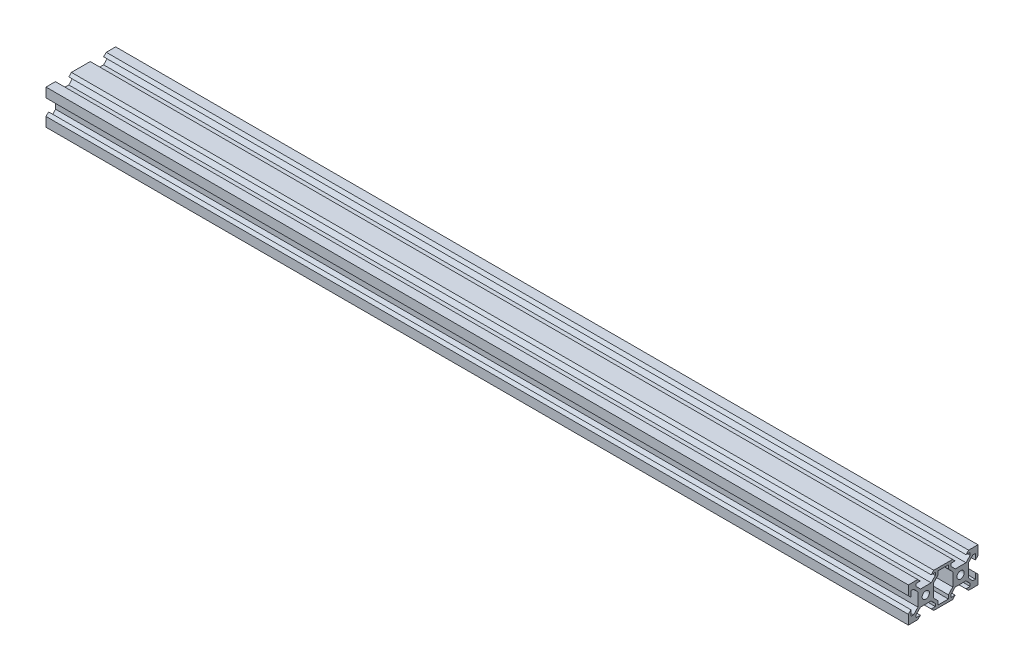
SolidWorks part; units mm, degrees
material "6061-T6 (SS)"
ref_plane "Front Plane" through (0, 0, 0) normal (0, 0, 1) x (1, 0, 0)
ref_plane "Top Plane" through (0, 0, 0) normal (0, 1, 0) x (1, 0, 0)
ref_plane "Right Plane" through (0, 0, 0) normal (1, 0, 0) x (0, 0, -1)
sketch "Sketch1" plane through (0, 0, 0) normal (1, 0, 0) x (0, 0, -1)
  line L136 (-20, -10) -> (-20, -4.6)
  line L147 (-20, -10) -> (20, -10) construction
  line L149 (-20, -10) -> (-20, 10) construction
  line L155 (-20, 10) -> (20, 10) construction
  line L156 (20, -10) -> (20, 10) construction
  line L162 (-20, -10) -> (20, 10) construction
  line L163 (-20, 10) -> (20, -10) construction
  line L177 (-20, -4.6) -> (-18.5, -3.1)
  line L180 (-14.5, -3.7924) -> (-14.5, 3.7924)
  line L181 (0, 0) -> (-20, 0) construction
  line L182 (0, 0) -> (0, -10) construction
  line L184 (-20, -10) -> (-14.6, -10)
  line L185 (-14.6, -10) -> (-13.1, -8.5)
  line L186 (-13.1, -8.5) -> (-15.5, -8.5)
  line L187 (-15.5, -8.5) -> (-15.5, -7)
  line L188 (-15.5, -7) -> (-13.1, -4.5)
  line L189 (-13.1, -4.5) -> (-6.9, -4.5)
  line L190 (-6.9, -4.5) -> (-4.5, -7)
  line L191 (-4.5, -7) -> (-4.5, -8.5)
  line L192 (-4.5, -8.5) -> (-6.9, -8.5)
  line L193 (-6.9, -8.5) -> (-5.4, -10)
  line L194 (-5.4, -10) -> (5.4, -10)
  line L195 (-3, -8.5) -> (-3, -6.3965)
  line L196 (-3, -8.5) -> (3, -8.5)
  line L197 (0, -8.5) -> (0, -10)
  line L201 (-14.5, 0) -> (-12.1, 0) construction
  line L203 (-7.9, 0) -> (-5.5, 0) construction
  line L204 (-5.5, 3.7924) -> (-5.5, -3.7924)
  line L205 (-5.5, -3.7924) -> (-3, -6.3965)
  line L206 (-13.1, -4.5) -> (-13.1, -8.5) construction
  line L207 (-13.1, -8.5) -> (-6.9, -8.5) construction
  line L208 (-6.9, -4.5) -> (-6.9, -8.5) construction
  line L209 (-18.5, -3.1) -> (-18.5, -6.3965)
  line L210 (-18.5, -6.3965) -> (-17, -6.3965)
  line L211 (-15.5, -7) -> (-4.5, -7) construction
  line L212 (-17, -6.3965) -> (-14.5, -3.7924)
  line L213 (-13.1, -4.5) -> (-6.9, -4.5) construction
  line L214 (-10, -4.5) -> (-10, 0) construction
  line L215 (-18.5, -6.3965) -> (-20, -6.3965) construction
  line L216 (-15.5, -8.5) -> (-15.5, -10) construction
  line L217 (-4.5, -8.5) -> (-4.5, -10) construction
  line L218 (-17, -6.3965) -> (-3, -6.3965) construction
  line L219 (-18.5, -3.1) -> (-20, -3.1) construction
  line L220 (-18.5, 6.3965) -> (-17, 6.3965)
  line L221 (-18.5, 3.1) -> (-18.5, 6.3965)
  line L222 (-20, 4.6) -> (-18.5, 3.1)
  line L223 (-20, 10) -> (-20, 4.6)
  line L224 (-20, 10) -> (-14.6, 10)
  line L225 (-14.6, 10) -> (-13.1, 8.5)
  line L226 (-13.1, 8.5) -> (-15.5, 8.5)
  line L227 (-15.5, 8.5) -> (-15.5, 7)
  line L228 (-15.5, 7) -> (-13.1, 4.5)
  line L229 (-13.1, 4.5) -> (-6.9, 4.5)
  line L230 (-6.9, 4.5) -> (-4.5, 7)
  line L231 (-4.5, 7) -> (-4.5, 8.5)
  line L232 (-4.5, 8.5) -> (-6.9, 8.5)
  line L233 (-6.9, 8.5) -> (-5.4, 10)
  line L234 (-5.4, 10) -> (5.4, 10)
  line L235 (0, 8.5) -> (0, 10)
  line L236 (-3, 8.5) -> (3, 8.5)
  line L237 (-3, 8.5) -> (-3, 6.3965)
  line L238 (-5.5, 3.7924) -> (-3, 6.3965)
  line L239 (-17, 6.3965) -> (-14.5, 3.7924)
  line L240 (18.5, 3.1) -> (18.5, 6.3965)
  line L241 (20, 4.6) -> (18.5, 3.1)
  line L242 (20, 10) -> (20, 4.6)
  line L243 (20, 10) -> (14.6, 10)
  line L244 (14.6, 10) -> (13.1, 8.5)
  line L245 (13.1, 8.5) -> (15.5, 8.5)
  line L246 (15.5, 8.5) -> (15.5, 7)
  line L247 (15.5, 7) -> (13.1, 4.5)
  line L248 (13.1, 4.5) -> (6.9, 4.5)
  line L249 (6.9, 4.5) -> (4.5, 7)
  line L250 (4.5, 7) -> (4.5, 8.5)
  line L251 (4.5, 8.5) -> (6.9, 8.5)
  line L252 (6.9, 8.5) -> (5.4, 10)
  line L253 (3, 8.5) -> (3, 6.3965)
  line L254 (5.5, 3.7924) -> (3, 6.3965)
  line L255 (5.5, 3.7924) -> (5.5, -3.7924)
  line L256 (5.5, -3.7924) -> (3, -6.3965)
  line L257 (3, -8.5) -> (3, -6.3965)
  line L258 (6.9, -8.5) -> (5.4, -10)
  line L259 (4.5, -8.5) -> (6.9, -8.5)
  line L260 (4.5, -7) -> (4.5, -8.5)
  line L261 (6.9, -4.5) -> (4.5, -7)
  line L262 (13.1, -4.5) -> (6.9, -4.5)
  line L263 (15.5, -7) -> (13.1, -4.5)
  line L264 (15.5, -8.5) -> (15.5, -7)
  line L265 (13.1, -8.5) -> (15.5, -8.5)
  line L266 (14.6, -10) -> (13.1, -8.5)
  line L267 (20, -10) -> (14.6, -10)
  line L268 (20, -10) -> (20, -4.6)
  line L269 (20, -4.6) -> (18.5, -3.1)
  line L270 (18.5, -3.1) -> (18.5, -6.3965)
  line L271 (18.5, -6.3965) -> (17, -6.3965)
  line L272 (17, -6.3965) -> (14.5, -3.7924)
  line L273 (14.5, -3.7924) -> (14.5, 3.7924)
  line L274 (17, 6.3965) -> (14.5, 3.7924)
  line L275 (18.5, 6.3965) -> (17, 6.3965)
  circle A1 centre (-10, 0) radius 2.1
  circle A2 centre (10, 0) radius 2.1
  point P0 (0, 0)
  dimension "D3" = 2.1
  dimension "D1" = 40
  dimension "D2" = 20
  dimension "D4" = 45
  dimension "D5" = 45
  dimension "D6" = 45
  dimension "D7" = 1.5
  dimension "D8" = 11
  dimension "D9" = 1.5
  dimension "D10" = 6.2
  dimension "D11" = 10
  dimension "D12" = 3.1
  dimension "D13" = 5.5
  dimension "D14" = 5.5
  dimension "D15" = 1.5
  dimension "D16" = 1.5
extrude "Boss-Extrude2" add sketch "Sketch1" along normal blind 495.3 contours L220 L239 L180 L212 L210 L209 L177 L136 L184 L185 L186 L187 L188 L189 L190 L191 L192 L193 L194 L197 L196 L195 L205 L204 L238 L237 L236 L235 L234 L233 L232 L231 L230 L229 L228 L227 L226 L225 L224 L223 L222 L221 A1 | L275 L240 L241 L242 L243 L244 L245 L246 L247 L248 L249 L250 L251 L252 L234 L235 L236 L253 L254 L255 L256 L257 L196 L197 L194 L258 L259 L260 L261 L262 L263 L264 L265 L266 L267 L268 L269 L270 L271 L272 L273 L274 A2
